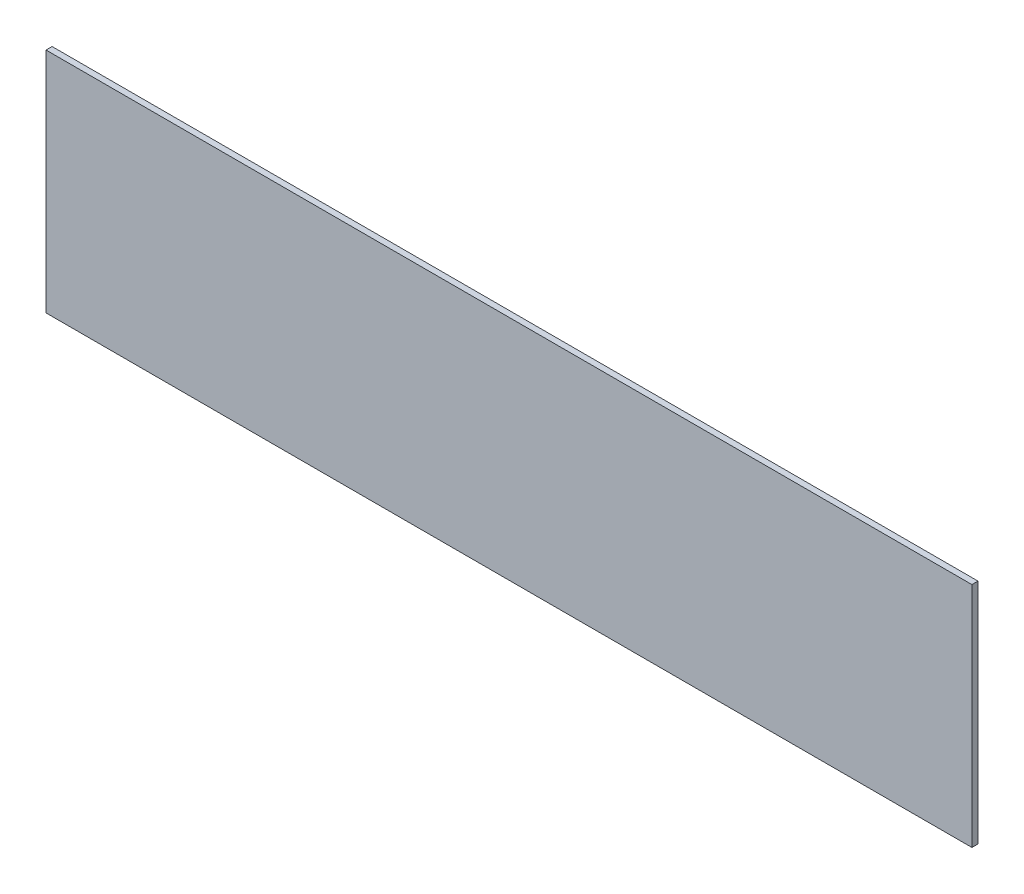
SolidWorks part; units mm, degrees
material "Acrílico (médio-alto impacto)"
ref_plane "Plano frontal" through (0, 0, 0) normal (0, 0, 1) x (1, 0, 0)
ref_plane "Plano superior" through (0, 0, 0) normal (0, 1, 0) x (1, 0, 0)
ref_plane "Plano direito" through (0, 0, 0) normal (1, 0, 0) x (0, 0, -1)
sketch "Esboço1" plane through (0, 0, 0) normal (0, 0, 1) x (1, 0, 0)
  line L1 (-305, -75) -> (305, -75)
  line L2 (-305, -75) -> (-305, 75)
  line L3 (-305, 75) -> (305, 75)
  line L4 (305, -75) -> (305, 75)
  line L5 (-305, -75) -> (305, 75) construction
  line L6 (-305, 75) -> (305, -75) construction
  point P0 (0, 0)
  dimension "D1" = 610
  dimension "D2" = 150
extrude "Ressalto-extrusão1" add sketch "Esboço1" along normal blind 4
